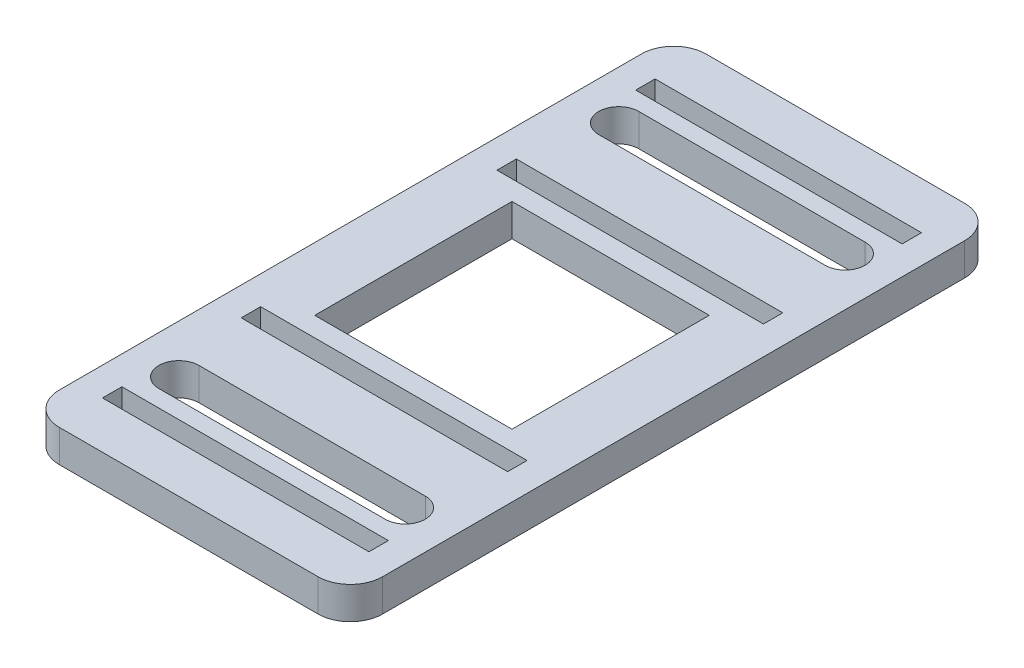
SolidWorks part; units mm, degrees
ref_plane "Front Plane" through (0, 0, 0) normal (0, 0, 1) x (1, 0, 0)
ref_plane "Top Plane" through (0, 0, 0) normal (0, 1, 0) x (1, 0, 0)
ref_plane "Right Plane" through (0, 0, 0) normal (1, 0, 0) x (0, 0, -1)
sketch "Sketch1" plane through (0, 0, 0) normal (0, 1, 0) x (1, 0, 0)
  line L1 (-25, 50) -> (25, 50)
  line L2 (-25, 50) -> (-25, -50)
  line L3 (-25, -50) -> (25, -50)
  line L4 (25, 50) -> (25, -50)
  line L5 (0, -50) -> (0, 50) construction
  line L6 (-25, 0) -> (25, 0) construction
  point P0 (0, 0)
  dimension "D1" = 50
  dimension "D2" = 100
extrude "Boss-Extrude1" add sketch "Sketch1" along normal blind 5
sketch "Sketch2" plane through (0, 5, 0) normal (0, 1, 0) x (1, 0, 0)
  line L0 (0, 50) -> (0, -50) construction
  line L1 (25, 50) -> (-25, 50) construction
  line L2 (-25, -50) -> (25, -50) construction
  line L3 (-17.5, -34.01) -> (17.5, -34.01) construction
  line L4 (-17.5, -30.91) -> (17.5, -30.91)
  line L5 (-17.5, -37.11) -> (17.5, -37.11)
  arc A0 (-17.5, -30.91) -> (-17.5, -37.11) centre (-17.5, -34.01) ccw
  arc A1 (17.5, -37.11) -> (17.5, -30.91) centre (17.5, -34.01) ccw
  point P8 (0, -34.01)
  dimension "D1" = 3.1
  dimension "D2" = 34.01
  dimension "D3" = 35
extrude "Cut-Extrude1" cut sketch "Sketch2" against normal through all and the other way through all
mirror "Mirror1" about plane through (0, 0, 0) normal (0, 0, 1) of "Cut-Extrude1"
fillet "Fillet1" radius 5 4 edges at (25, 2.5, -50) (-25, 2.5, -50) (25, 2.5, 50) (-25, 2.5, 50)
sketch "Sketch3" plane through (0, 5, 0) normal (0, 1, 0) x (1, 0, 0)
  line L1 (-15.25, -15.25) -> (15.25, -15.25)
  line L2 (-15.25, -15.25) -> (-15.25, 15.25)
  line L3 (-15.25, 15.25) -> (15.25, 15.25)
  line L4 (15.25, -15.25) -> (15.25, 15.25)
  line L5 (0, 15.25) -> (0, -15.25) construction
  line L6 (-15.25, 0) -> (15.25, 0) construction
  point P0 (0, 0)
  dimension "D1" = 30.5
extrude "Cut-Extrude2" cut sketch "Sketch3" against normal through all
sketch "Sketch4" plane through (0, 5, 0) normal (0, 1, 0) x (1, 0, 0)
  line L0 (0, 50) -> (0, -50) construction
  line L1 (20, 50) -> (-20, 50) construction
  line L2 (-20, -50) -> (20, -50) construction
  line L3 (-15.25, -15.25) -> (15.25, -15.25) construction
  line L4 (-20.6, -21.275) -> (20.6, -21.275)
  line L5 (-20.6, -21.275) -> (-20.6, -18.275)
  line L6 (-20.6, -18.275) -> (20.6, -18.275)
  line L7 (20.6, -21.275) -> (20.6, -18.275)
  line L8 (0, -18.275) -> (0, -21.275) construction
  line L9 (-20.6, -19.775) -> (20.6, -19.775) construction
  line L11 (-20.6, -39.725) -> (20.6, -39.725)
  line L12 (-20.6, -39.725) -> (-20.6, -42.725)
  line L13 (-20.6, -42.725) -> (20.6, -42.725)
  line L14 (20.6, -39.725) -> (20.6, -42.725)
  line L15 (0, -42.725) -> (0, -39.725) construction
  line L16 (-20.6, -41.225) -> (20.6, -41.225) construction
  point P6 (0, -19.775)
  point P12 (0, -41.225)
  dimension "D1" = 3
  dimension "D2" = 4.525
  dimension "D3" = 25.975
  dimension "D4" = 41.2
extrude "Cut-Extrude3" cut sketch "Sketch4" against normal through all and the other way through all
mirror "Mirror2" about plane through (0, 0, 0) normal (0, 0, 1) of "Cut-Extrude3"
